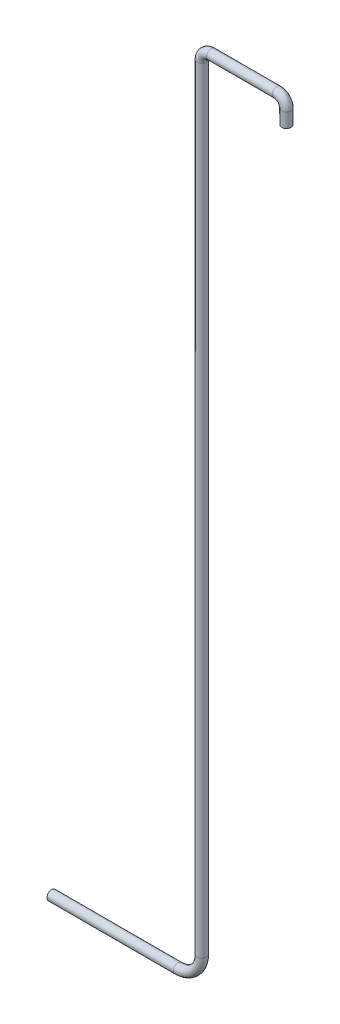
SolidWorks part; units mm, degrees
ref_plane "Plan de face" through (0, 0, 0) normal (0, 0, 1) x (1, 0, 0)
ref_plane "Plan de dessus" through (0, 0, 0) normal (0, 1, 0) x (1, 0, 0)
ref_plane "Plan de droite" through (0, 0, 0) normal (1, 0, 0) x (0, 0, -1)
sketch "Esquisse1" plane through (0, 0, 0) normal (0, 0, 1) x (1, 0, 0)
  line L0 (0, 0) -> (0, 0.3)
  line L1 (-0.2, 0.5) -> (-1.5845, 0.5)
  line L2 (-1.7845, 0.3) -> (-1.7845, -16.05)
  line L3 (-2.2845, -16.55) -> (-4.9545, -16.55)
  arc A0 (-1.7845, 0.3) -> (-1.5845, 0.5) centre (-1.5845, 0.3) cw
  arc A1 (-0.2, 0.5) -> (0, 0.3) centre (-0.2, 0.3) cw
  arc A2 (-2.2845, -16.55) -> (-1.7845, -16.05) centre (-2.2845, -16.05) ccw
  dimension "D1" = 0.2
  dimension "D2" = 0.5
sketch "Esquisse2" plane through (0, 0, 0) normal (0, 1, 0) x (1, 0, 0)
  circle A0 centre (0, 0) radius 0.1
sweep "Balayage1" add profiles "Esquisse2" path "Esquisse1"
